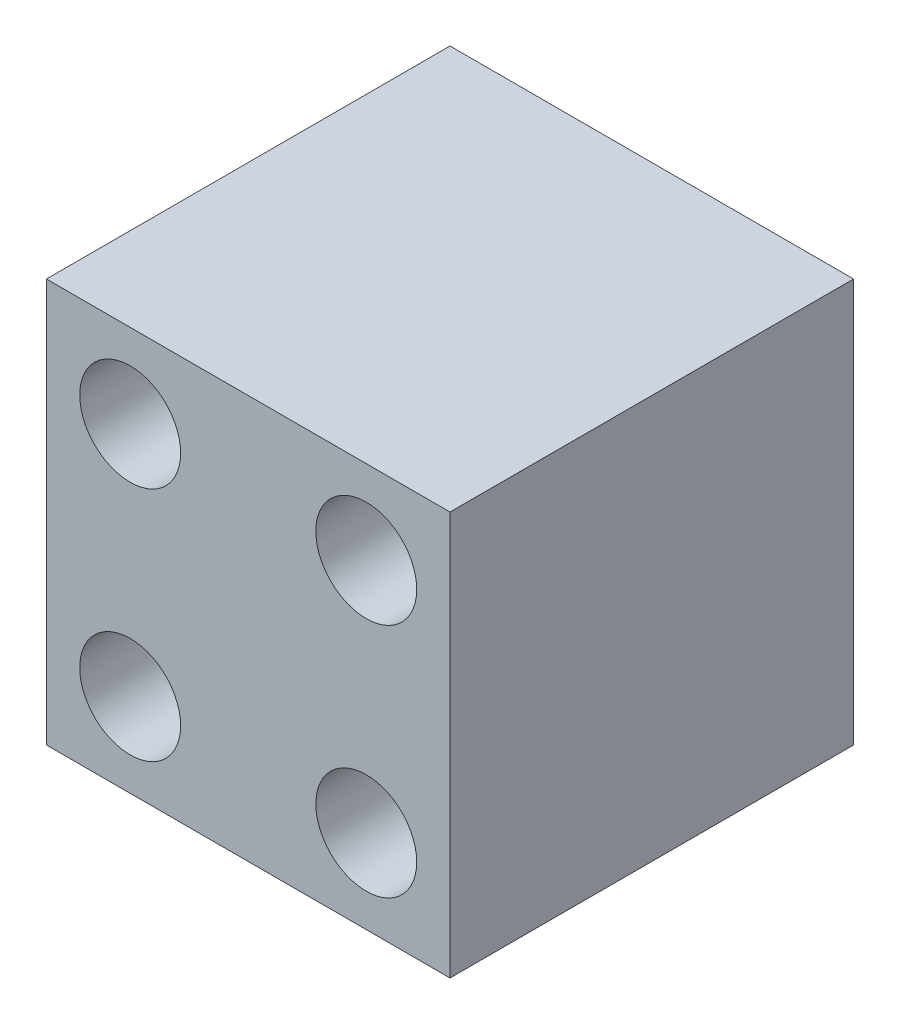
SolidWorks part; units mm, degrees
ref_plane "Front Plane" through (0, 0, 0) normal (0, 0, 1) x (1, 0, 0)
ref_plane "Top Plane" through (0, 0, 0) normal (0, 1, 0) x (1, 0, 0)
ref_plane "Right Plane" through (0, 0, 0) normal (1, 0, 0) x (0, 0, -1)
sketch "Sketch1" plane through (0, 0, 0) normal (0, 0, 1) x (1, 0, 0)
  line L0 (31.7, 40) -> (31.7, 31.7) construction
  line L1 (0, 0) -> (40, 0)
  line L2 (0, 0) -> (0, 40)
  line L3 (0, 40) -> (40, 40)
  line L4 (40, 0) -> (40, 40)
  line L5 (31.7, 8.3) -> (31.7, 0) construction
  line L6 (8.3, 8.3) -> (0, 8.3) construction
  line L7 (31.7, 8.3) -> (40, 8.3) construction
  circle A0 centre (8.3, 31.7) radius 5
  circle A1 centre (31.7, 31.7) radius 5
  circle A2 centre (8.3, 8.3) radius 5
  circle A3 centre (31.7, 8.3) radius 5
  dimension "D2" = 10
  dimension "D1" = 40
  dimension "D3" = 23.4
  dimension "D4" = 23.4
extrude "Boss-Extrude1" add sketch "Sketch1" along normal blind 40
